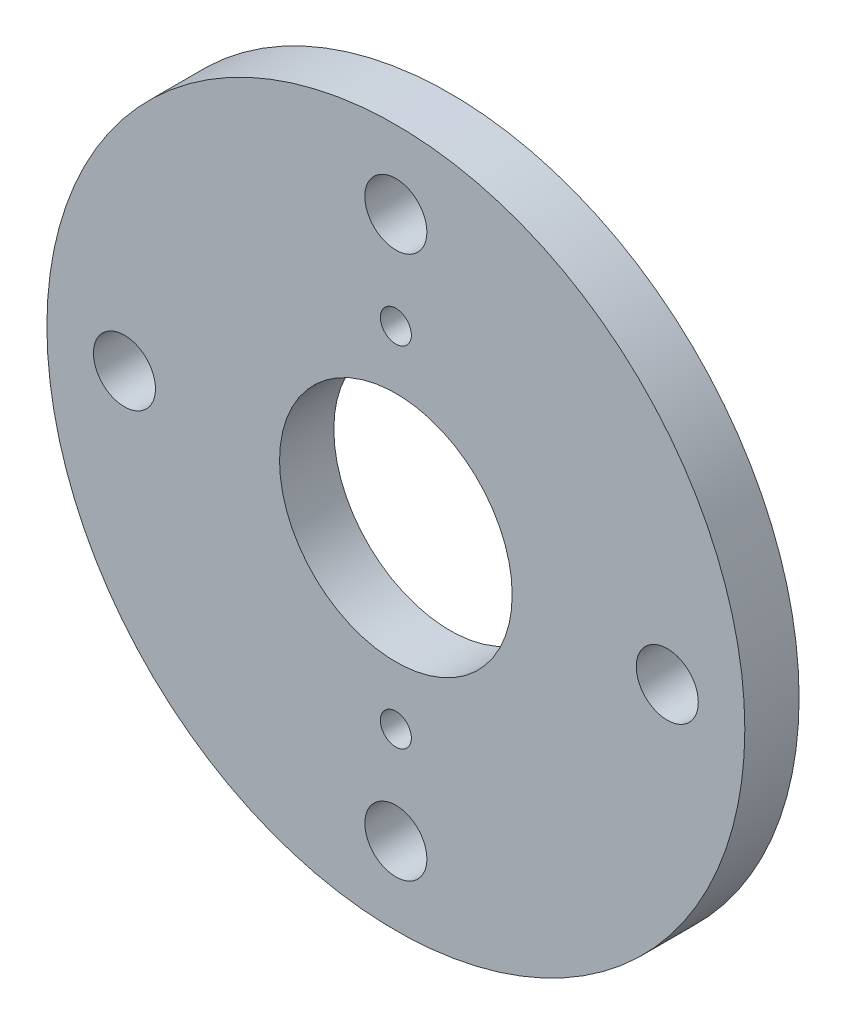
SolidWorks part; units mm, degrees
ref_plane "Alzado" through (0, 0, 0) normal (0, 0, 1) x (1, 0, 0)
ref_plane "Planta" through (0, 0, 0) normal (0, 1, 0) x (1, 0, 0)
ref_plane "Vista lateral" through (0, 0, 0) normal (1, 0, 0) x (0, 0, -1)
sketch "Croquis1" plane through (0, 0, 0) normal (0, 0, 1) x (1, 0, 0)
  circle A0 centre (0, 0) radius 45
  dimension "D1" = 90
extrude "Saliente-Extruir1" add sketch "Croquis1" along normal blind 7
sketch "Croquis2" plane through (0, 0, 7) normal (0, 0, 1) x (1, 0, 0)
  circle A0 centre (0, 0) radius 15
  dimension "D1" = 30
extrude "Cortar-Extruir1" cut sketch "Croquis2" against normal through all
sketch "Croquis3" plane through (0, 0, 7) normal (0, 0, 1) x (1, 0, 0)
  line L0 (45, 0) -> (-45, 0) construction
  line L1 (0, 45) -> (0, -45) construction
  circle A0 centre (0, 0) radius 45 construction
  circle A2 centre (0, 35) radius 4
  circle A3 centre (35, 0) radius 4
  circle A4 centre (0, -35) radius 4
  circle A5 centre (-35, 0) radius 4
  circle A6 centre (0, 0) radius 35 construction
  point P20 (0, 0)
  dimension "D1" = 70
  dimension "D3" = 8
  dimension "D2" = 4
extrude "Cortar-Extruir2" cut sketch "Croquis3" against normal through all
sketch "Croquis4" plane through (0, 0, 7) normal (0, 0, 1) x (1, 0, 0)
  line L0 (0, 22.5) -> (0, -22.5) construction
  circle A0 centre (0, 22.5) radius 2
  circle A1 centre (0, -22.5) radius 2
  point P5 (0, 0)
  dimension "D2" = 4
  dimension "D1" = 45
extrude "Cortar-Extruir3" cut sketch "Croquis4" against normal through all
